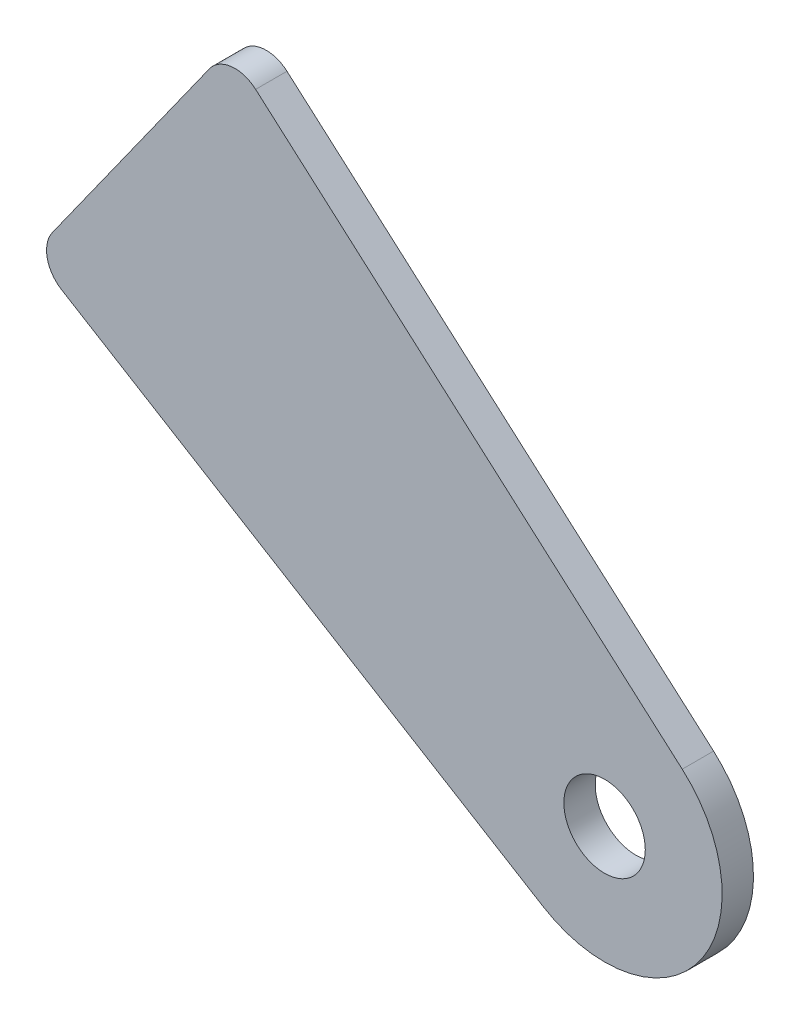
SolidWorks part; units mm, degrees
material "ASTM A36 Steel"
ref_plane "Front Plane" through (0, 0, 0) normal (0, 0, 1) x (1, 0, 0)
ref_plane "Top Plane" through (0, 0, 0) normal (0, 1, 0) x (1, 0, 0)
ref_plane "Right Plane" through (0, 0, 0) normal (1, 0, 0) x (0, 0, -1)
sketch "Sketch1" plane through (0, 0, 0) normal (0, 0, 1) x (1, 0, 0)
  line L0 (32.1903, -35.282) -> (-9.1733, -10.0799)
  line L1 (43.4392, -19.9977) -> (6.765, 12.2796)
  line L2 (-9.1733, -10.0799) -> (6.765, 12.2796)
  circle A2 centre (37.1463, -27.1479) radius 3.3
  circle A4 centre (37.1463, -27.1479) radius 9.525 construction
  arc A6 (43.4392, -19.9977) -> (32.1903, -35.282) centre (37.1463, -27.1479) cw
  point P0 (0, 0)
  dimension "D4" = 19.05
  dimension "D5" = 6.6
  dimension "D1" = 47.625
extrude "Boss-Extrude3" add sketch "Sketch1" along normal blind 2.54
fillet "Fillet1" radius 2.54 1 edges at (-9.1733, -10.0799, 1.27)
fillet "Fillet2" radius 2.54 1 edges at (6.765, 12.2796, 1.27)
